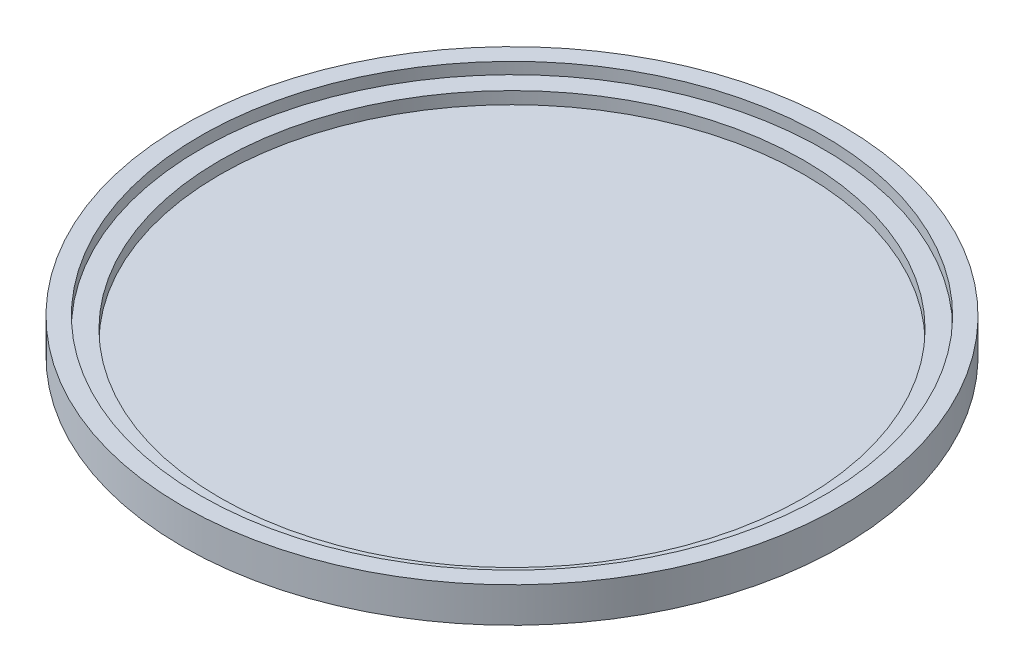
SolidWorks part; units mm, degrees
ref_plane "Plano frontal" through (0, 0, 0) normal (0, 0, 1) x (1, 0, 0)
ref_plane "Plano superior" through (0, 0, 0) normal (0, 1, 0) x (1, 0, 0)
ref_plane "Plano direito" through (0, 0, 0) normal (1, 0, 0) x (0, 0, -1)
sketch "Esboço1" plane through (0, 0, 0) normal (0, 1, 0) x (1, 0, 0)
  circle A0 centre (0, 0) radius 154
  dimension "D1" = 308
extrude "Ressalto-extrusão1" add sketch "Esboço1" along normal blind 16.4
sketch "Esboço2" plane through (0, 16.4, 0) normal (0, 1, 0) x (1, 0, 0)
  circle A2 centre (0, 0) radius 145.6
  circle A3 centre (0, 0) radius 145.6
  dimension "D1" = 8.4
extrude "Corte-extrusão1" cut sketch "Esboço2" against normal blind 5.4 contours A3
sketch "Esboço3" plane through (0, 11, 0) normal (0, 1, 0) x (1, 0, 0)
  circle A2 centre (0, 0) radius 136.5
  circle A3 centre (0, 0) radius 136.5
  dimension "D1" = 9.1
extrude "Corte-extrusão2" cut sketch "Esboço3" against normal blind 5.72
sketch "Esboço4" plane through (0, 0, 0) normal (0, -1, 0) x (1, 0, 0)
  circle A2 centre (0, 0) radius 152.8
  circle A3 centre (0, 0) radius 152.8
  dimension "D1" = 1.2
extrude "Corte-extrusão5" cut sketch "Esboço4" against normal offset from surface (4.08 mm away) 1.2 contours A3 up to face at (0, 5.28, 136.5)
